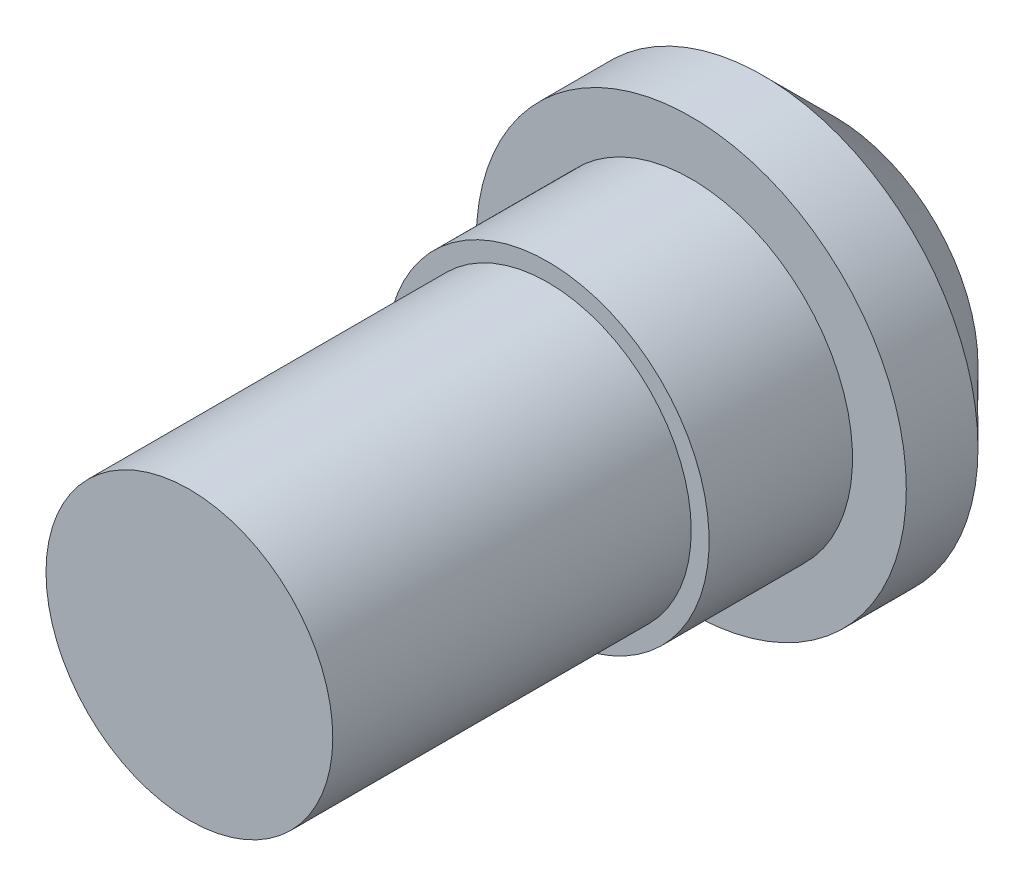
SolidWorks part; units mm, degrees
material "AISI 1020"
ref_plane "Спереди" through (0, 0, 0) normal (0, 0, 1) x (1, 0, 0)
ref_plane "Сверху" through (0, 0, 0) normal (0, 1, 0) x (1, 0, 0)
ref_plane "Справа" through (0, 0, 0) normal (1, 0, 0) x (0, 0, -1)
sketch "Эскиз1" plane through (0, 0, 0) normal (1, 0, 0) x (0, 0, -1)
  line L0 (0, 0) -> (-15.7464, 0) construction
  line L1 (0, 0) -> (0, 4)
  line L2 (0, 20.7852) -> (0, -21) construction
  line L3 (0, 4) -> (-2, 6)
  line L4 (0, 6) -> (-4, 6) construction
  line L5 (-2, 6) -> (-4, 6)
  line L6 (-4, 6) -> (-4, 4.5)
  line L7 (-4, 13.5) -> (-4, -15.188) construction
  line L8 (-4, 4.5) -> (-8, 4.5)
  line L9 (-18, 4) -> (-18, 0)
  line L10 (-18, 4) -> (-8, 4)
  line L11 (-8, 13.5) -> (-8, -15.188) construction
  line L12 (0, 0) -> (-18, 0)
  line L13 (-8, 4) -> (-8, 4.5)
  dimension "D1" = 1.5
  dimension "D2" = 2
  dimension "D3" = 9
  dimension "D4" = 10
  dimension "D5" = 10
revolve "Повернуть1" add sketch "Эскиз1" angle 360 about L0
cosmetic thread "Условное изображение резьбы1" parameters "D2"=6.619
